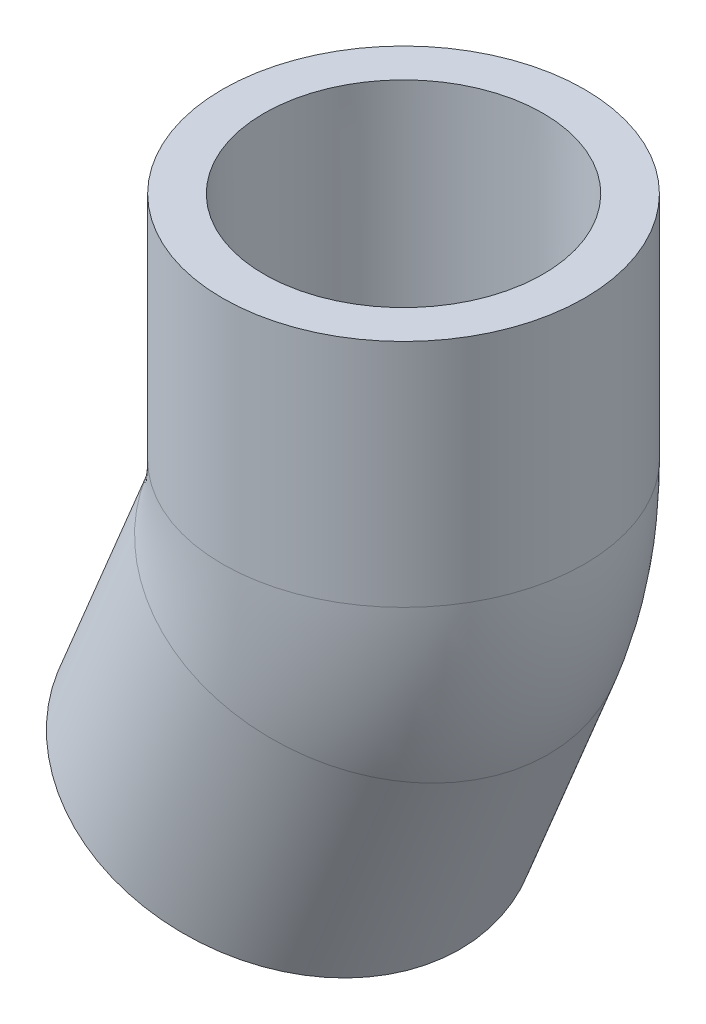
SolidWorks part; units mm, degrees
ref_plane "Front Plane" through (0, 0, 0) normal (0, 0, 1) x (1, 0, 0)
ref_plane "Top Plane" through (0, 0, 0) normal (0, 1, 0) x (1, 0, 0)
ref_plane "Right Plane" through (0, 0, 0) normal (1, 0, 0) x (0, 0, -1)
sketch "Sketch0" plane through (0, 0, 0) normal (0, 0, 1) x (1, 0, 0)
  line L0 (-13.3652, -32.2665) -> (0, 0) construction
  line L1 (0, 0) -> (0, 34.925) construction
  line L2 (-2.7338, -6.6) -> (0, 0) construction
  line L3 (0, 0) -> (0, 7.1438) construction
  line L4 (-33.5318, -23.9132) -> (6.8013, -40.6198) construction
  line L5 (-18.1044, -0.2333) -> (-28.9118, -25.8269) construction
  line L6 (-18.1044, -0.2333) -> (12.6368, -12.9667) construction
  line L7 (12.6368, -12.9667) -> (2.1814, -38.7061) construction
  line L8 (-28.9118, -25.8269) -> (2.1814, -38.7061) construction
  line L9 (-21.8281, 34.925) -> (21.8281, 34.925) construction
  line L10 (-16.8275, 34.925) -> (16.8275, 34.925) construction
  line L11 (16.8275, 34.925) -> (16.637, 7.1437) construction
  line L12 (16.637, 7.1437) -> (-16.637, 7.1437) construction
  line L13 (-16.637, 7.1437) -> (-16.8275, 34.925) construction
  line L14 (-15.042, -1.5017) -> (9.5744, -11.6982) construction
  line L18 (-13.3223, 7.1437) -> (13.3223, 7.1437) construction
  dimension "H" = 34.925
  dimension "J" = 7.1437
  dimension "M" = 43.6562
  dimension "OD A" = 33.655
  dimension "OD B" = 33.274
  dimension "ID" = 26.6446
  dimension "A" = 22.5
sketch "Sketch1" plane through (0, 0, 0) normal (0, 0, 1) x (1, 0, 0)
  line L0 (-13.3652, -32.2665) -> (0, 0) construction
  line L1 (-13.3652, -32.2665) -> (0, 0) construction
  line L3 (6.8013, -40.6198) -> (17.4328, -14.9532)
  line L4 (6.8013, -40.6198) -> (2.1814, -38.7061)
  line L5 (2.1814, -38.7061) -> (12.6368, -12.9667)
  line L6 (17.4328, -14.9532) -> (12.6368, -12.9667)
revolve "Revolve1" add sketch "Sketch1" angle 360 about L1
sketch "Sketch2" plane through (0, 0, 0) normal (0, 0, 1) x (1, 0, 0)
  line L0 (16.8275, 34.925) -> (16.637, 7.1437)
  line L1 (16.637, 7.1437) -> (21.8281, 7.1437)
  line L2 (21.8281, 7.1437) -> (21.8281, 34.925)
  line L3 (21.8281, 34.925) -> (16.8275, 34.925)
  line L4 (0, 0) -> (0, 34.925) construction
  line L5 (0, 0) -> (0, 34.925) construction
revolve "Revolve2" add sketch "Sketch2" angle 360 about L5
sketch "Sketch3" plane through (-2.7338, -6.6, 0) normal (0.3827, 0.9239, 0) x (0, 0, -1)
  circle A0 centre (0, 0) radius 13.3223
  circle A1 centre (0, 0) radius 21.8281
sketch "Sketch4" plane through (0, 0, 0) normal (0, 0, 1) x (1, 0, 0)
  line L0 (-13.3652, -32.2665) -> (0, 0) construction
  line L1 (0, 0) -> (0, 34.925) construction
  line L2 (-13.3652, -32.2665) -> (-2.7338, -6.6) construction
  line L3 (0, 7.1437) -> (0, 34.925) construction
  arc A0 (-2.7338, -6.6) -> (0, 7.1437) centre (-35.9141, 7.1437) ccw
sweep "Sweep1" add profiles "Sketch3" path "Sketch4"
